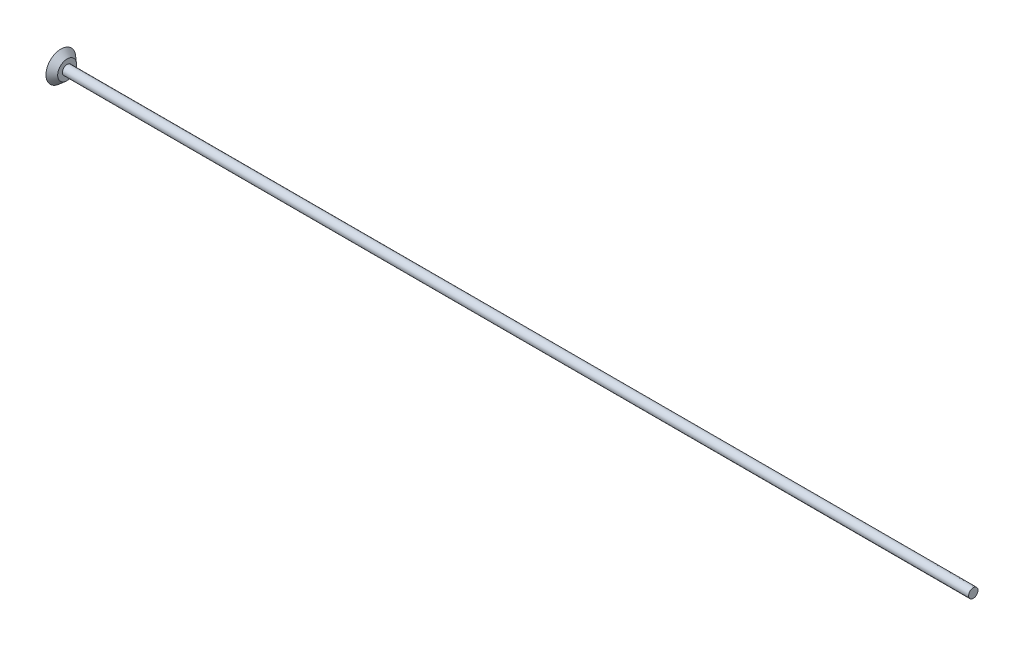
SolidWorks part; units mm, degrees
ref_plane "Front Plane" through (0, 0, 0) normal (0, 0, 1) x (1, 0, 0)
ref_plane "Top Plane" through (0, 0, 0) normal (0, 1, 0) x (1, 0, 0)
ref_plane "Right Plane" through (0, 0, 0) normal (1, 0, 0) x (0, 0, -1)
sketch "Sketch1" plane through (0, 0, 0) normal (0, 1, 0) x (1, 0, 0)
  line L0 (0, 0) -> (0, 4.7625)
  line L1 (0, 4.7625) -> (2, 3.0136)
  line L2 (2, 3.0136) -> (2, 1.5)
  line L3 (2, 1.5) -> (292.0307, 1.5)
  line L4 (292.0307, 1.5) -> (292.0307, 0)
  line L5 (292.0307, 0) -> (0, 0)
  point P3 (2, 3.0136)
  dimension "D1" = 1.5
  dimension "D2" = 4.7625
  dimension "D3" = 2
revolve "Revolve1" add sketch "Sketch1" angle 360 about L5
